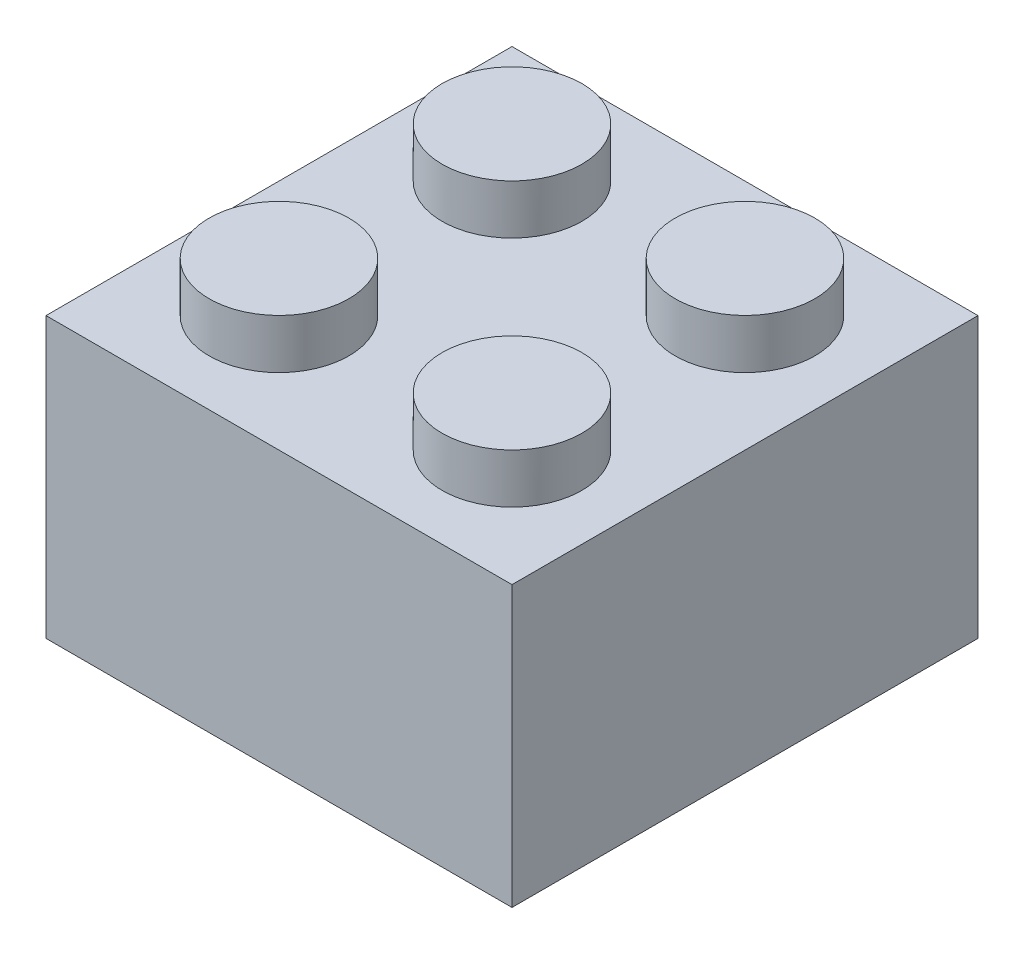
SolidWorks part; units mm, degrees
ref_plane "前基準面" through (0, 0, 0) normal (0, 0, 1) x (1, 0, 0)
ref_plane "上基準面" through (0, 0, 0) normal (0, 1, 0) x (1, 0, 0)
ref_plane "右基準面" through (0, 0, 0) normal (1, 0, 0) x (0, 0, -1)
sketch "草圖1" plane through (0, 0, 0) normal (0, 1, 0) x (1, 0, 0)
  line L0 (0, 18.3273) -> (0, -19.5636) construction
  line L1 (-8, -8) -> (8, -8)
  line L2 (-8, -8) -> (-8, 8)
  line L3 (-8, 8) -> (8, 8)
  line L4 (8, -8) -> (8, 8)
  line L5 (-8, -8) -> (8, 8) construction
  line L6 (-8, 8) -> (8, -8) construction
  line L8 (-16.5091, 0) -> (17.5273, 0) construction
  point P0 (0, 0)
  dimension "D1" = 16
  dimension "D2" = 16
extrude "height" add sketch "草圖1" along normal blind 9.6
sketch "草圖2" plane through (0, 9.6, 0) normal (0, 1, 0) x (1, 0, 0)
  line L0 (0, 10.2385) -> (0, -10.0857) construction
  line L2 (-12.1946, 0) -> (12.1946, 0) construction
  line L3 (-4, -4) -> (4, -4) construction
  line L4 (-4, -4) -> (-4, 4) construction
  line L5 (-4, 4) -> (4, 4) construction
  line L6 (4, -4) -> (4, 4) construction
  line L7 (-4, -4) -> (4, 4) construction
  line L8 (-4, 4) -> (4, -4) construction
  circle A0 centre (-4, 4) radius 2.4
  circle A1 centre (4, 4) radius 2.4
  circle A2 centre (4, -4) radius 2.4
  circle A3 centre (-4, -4) radius 2.4
  point P7 (0, 0)
  dimension "D3" = 4.8
  dimension "D1" = 8
  dimension "D2" = 8
extrude "填料-伸長2" add sketch "草圖2" along normal blind 1.7
shell "薄殼1" thickness 1.6
sketch "草圖3" plane through (0, 8, 0) normal (0, -1, 0) x (1, 0, 0)
  circle A0 centre (0, 0) radius 2.4
  circle A1 centre (0, 0) radius 3.255
  dimension "D1" = 4.8
  dimension "D2" = 6.51
extrude "填料-伸長3" add sketch "草圖3" along normal up to surface (8 mm away) up to face at (0, 0, 0)
